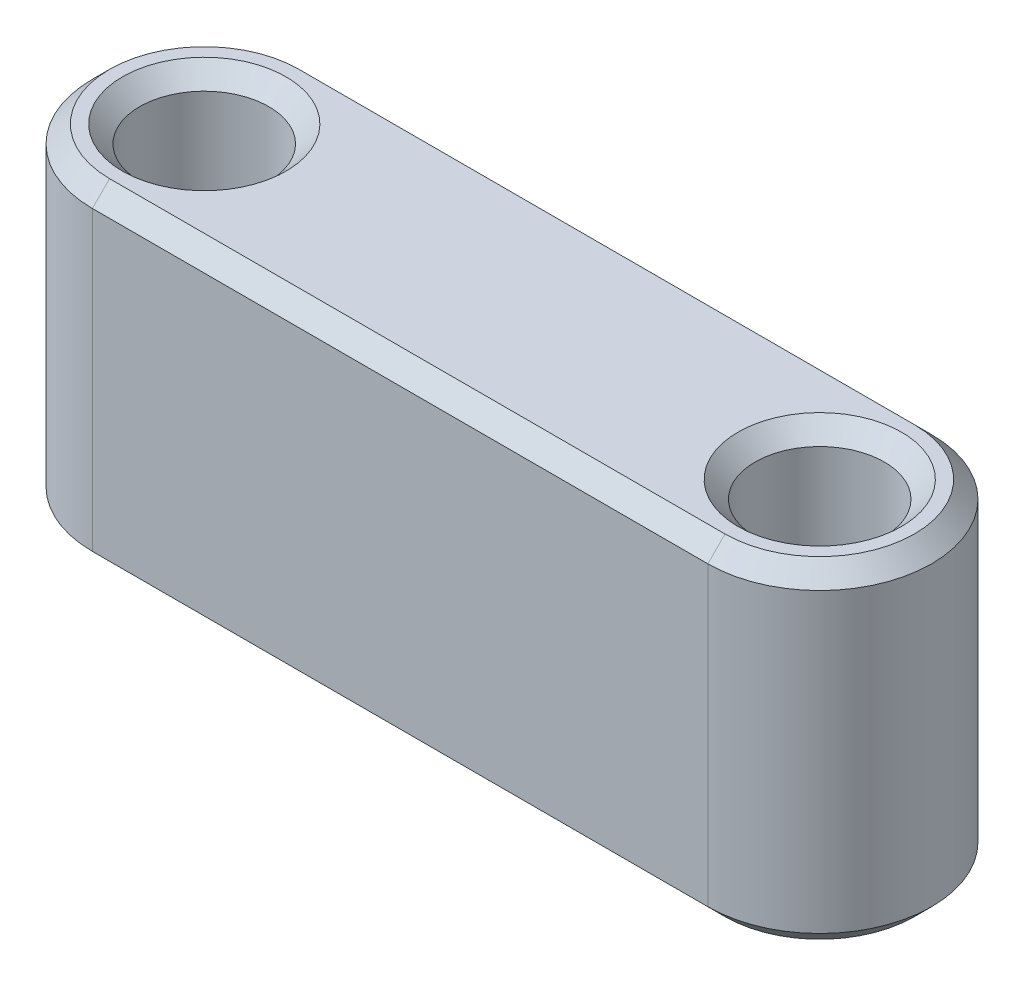
SolidWorks part; units mm, degrees
ref_plane "Front Plane" through (0, 0, 0) normal (0, 0, 1) x (1, 0, 0)
ref_plane "Top Plane" through (0, 0, 0) normal (0, 1, 0) x (1, 0, 0)
ref_plane "Right Plane" through (0, 0, 0) normal (1, 0, 0) x (0, 0, -1)
sketch "Sketch1" plane through (0, 0, 0) normal (0, 1, 0) x (1, 0, 0)
  line L0 (-12.6482, 0) -> (16.163, 0) construction
  line L1 (-5.9636, 0) -> (8.3364, 0) construction
  line L2 (-5.9636, 2.6) -> (8.3364, 2.6)
  line L3 (-5.9636, -2.6) -> (8.3364, -2.6)
  line L4 (1.1864, 6.0366) -> (1.1864, -10.7593) construction
  arc A0 (-5.9636, 2.6) -> (-5.9636, -2.6) centre (-5.9636, 0) ccw
  arc A1 (8.3364, -2.6) -> (8.3364, 2.6) centre (8.3364, 0) ccw
  circle A2 centre (-5.9636, 0) radius 1.5
  circle A4 centre (8.3364, 0) radius 1.5
  point P5 (1.1864, 0)
  point P10 (-8.5636, 0)
  point P11 (10.9364, 0)
  dimension "D3" = 3
  dimension "D1" = 19.5
  dimension "D2" = 5.2
  dimension "D4" = 14.3
extrude "Boss-Extrude1" add sketch "Sketch1" along normal mid plane 7.7
chamfer "Chamfer2" distance 0.4 angle 45 12 edges at (8.3364, -3.85, -1.5) (-5.9636, -3.85, 1.5) (1.1864, -3.85, 2.6) (10.9364, -3.85, 0) (-8.5636, -3.85, 0) (1.1864, -3.85, -2.6) (8.3364, 3.85, -1.5) (-5.9636, 3.85, 1.5) (10.9364, 3.85, 0) (1.1864, 3.85, 2.6) (-8.5636, 3.85, 0) (1.1864, 3.85, -2.6)
